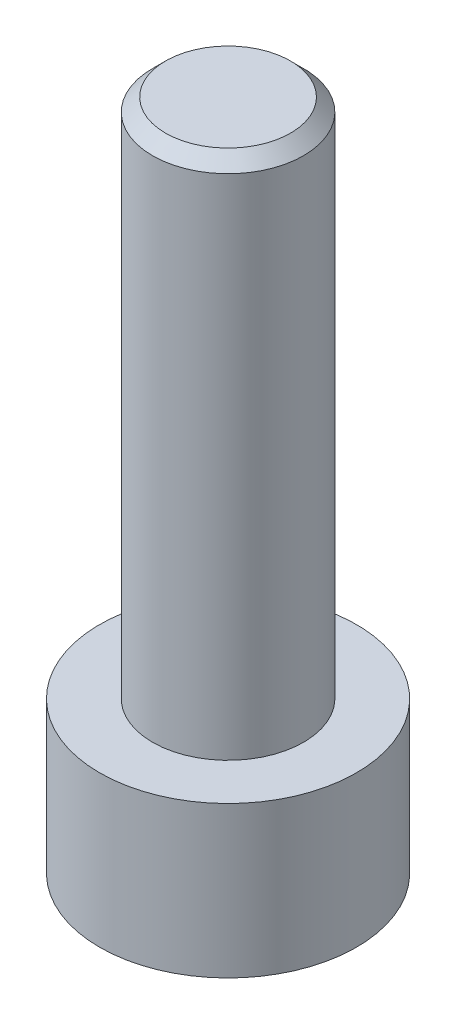
SolidWorks part; units mm, degrees
material "201 Annealed Stainless Steel (SS)"
ref_plane "Front Plane" through (0, 0, 0) normal (0, 0, 1) x (1, 0, 0)
ref_plane "Top Plane" through (0, 0, 0) normal (0, 1, 0) x (1, 0, 0)
ref_plane "Right Plane" through (0, 0, 0) normal (1, 0, 0) x (0, 0, -1)
sketch "Sketch1" plane through (0, 0, 0) normal (0, 1, 0) x (1, 0, 0)
  circle A0 centre (0, 0) radius 2.465
  dimension "D1" = 4.93
extrude "Boss-Extrude1" add sketch "Sketch1" along normal blind 2.9
sketch "Sketch2" plane through (0, 2.9, 0) normal (0, 1, 0) x (1, 0, 0)
  circle A0 centre (0, 0) radius 1.45
  dimension "D1" = 2.9
extrude "Boss-Extrude2" add sketch "Sketch2" along normal blind 10
sketch "Sketch3" plane through (0, 0, 0) normal (0, -1, 0) x (1, 0, 0)
  line L1 (0.7332, -1.27) -> (1.4665, 0)
  line L2 (1.4665, 0) -> (0.7332, 1.27)
  line L3 (0.7332, 1.27) -> (-0.7332, 1.27)
  line L4 (-0.7332, 1.27) -> (-1.4665, 0)
  line L5 (-1.4665, 0) -> (-0.7332, -1.27)
  line L6 (-0.7332, -1.27) -> (0.7332, -1.27)
  circle A0 centre (0, 0) radius 1.27 construction
  dimension "D1" = 2.54
extrude "Cut-Extrude1" cut sketch "Sketch3" against normal blind 1.9
chamfer "Chamfer1" distance 0.25 angle 45 1 edges at (0, 12.9, 1.45)
